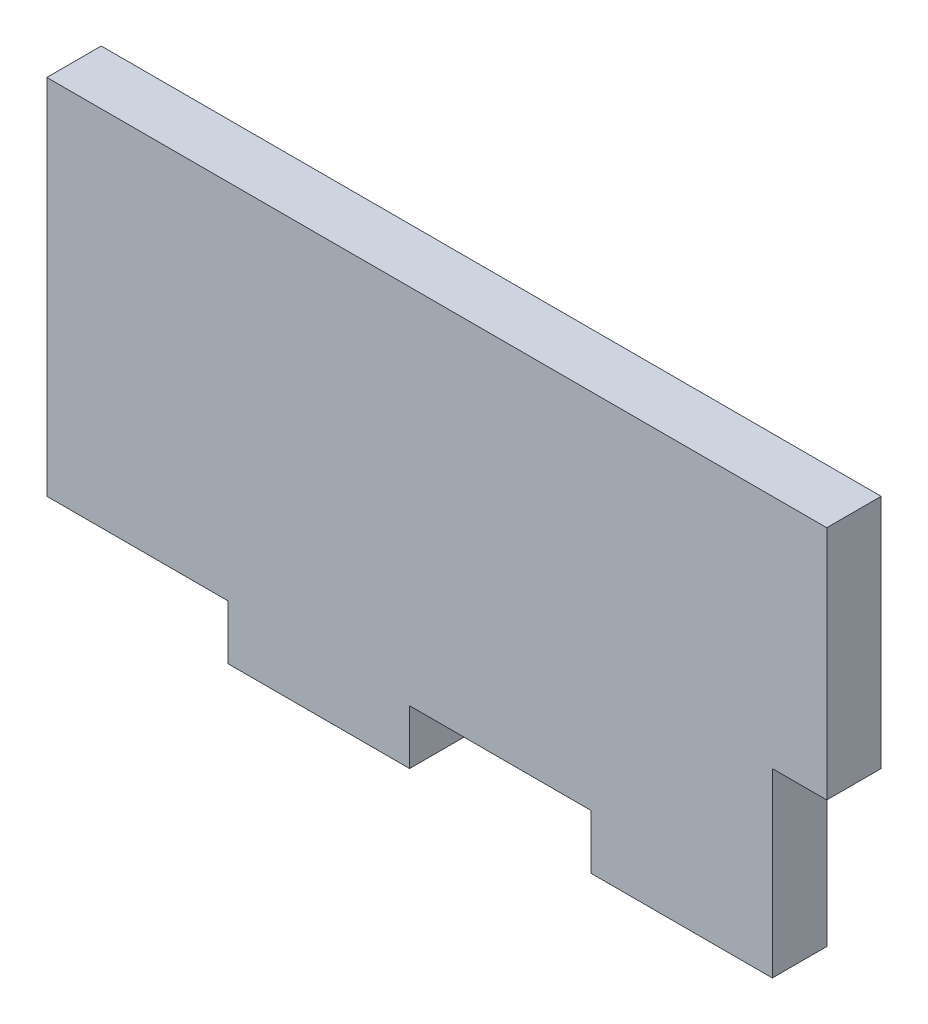
SolidWorks part; units mm, degrees
ref_plane "Plan de face" through (0, 0, 0) normal (0, 0, 1) x (1, 0, 0)
ref_plane "Plan de dessus" through (0, 0, 0) normal (0, 1, 0) x (1, 0, 0)
ref_plane "Plan de droite" through (0, 0, 0) normal (1, 0, 0) x (0, 0, -1)
sketch "Esquisse1" plane through (0, 0, 0) normal (0, 0, 1) x (1, 0, 0)
  line L1 (0, 0) -> (43, 0)
  line L2 (0, 0) -> (0, -23)
  line L3 (0, -23) -> (43, -23)
  line L4 (43, 0) -> (43, -23)
  dimension "D1" = 43
  dimension "D2" = 23
extrude "Boss.-Extru.1" add sketch "Esquisse1" along normal blind 3
sketch "Esquisse2" plane through (43, 0, 0) normal (1, 0, 0) x (0, 0, -1)
  line L0 (0, -23) -> (0, 0) construction
  line L1 (-3, -23) -> (0, -23)
  line L2 (-3, -23) -> (-3, -13)
  line L3 (-3, -13) -> (0, -13)
  line L4 (0, -23) -> (0, -13)
  dimension "D1" = 10
extrude "Enlèv. mat.-Extru.1" cut sketch "Esquisse2" against normal blind 3
sketch "Esquisse3" plane through (0, 0, 3) normal (0, 0, 1) x (1, 0, 0)
  line L1 (0, -23) -> (10, -23)
  line L2 (0, -23) -> (0, -20)
  line L3 (0, -20) -> (10, -20)
  line L4 (10, -23) -> (10, -20)
  dimension "D1" = 10
  dimension "D2" = 3
extrude "Enlèv. mat.-Extru.2" cut sketch "Esquisse3" against normal blind 3
pattern_linear "Répétition linéaire1" count 2 spacing 20 along (1, 0, 0) of "Enlèv. mat.-Extru.2"
